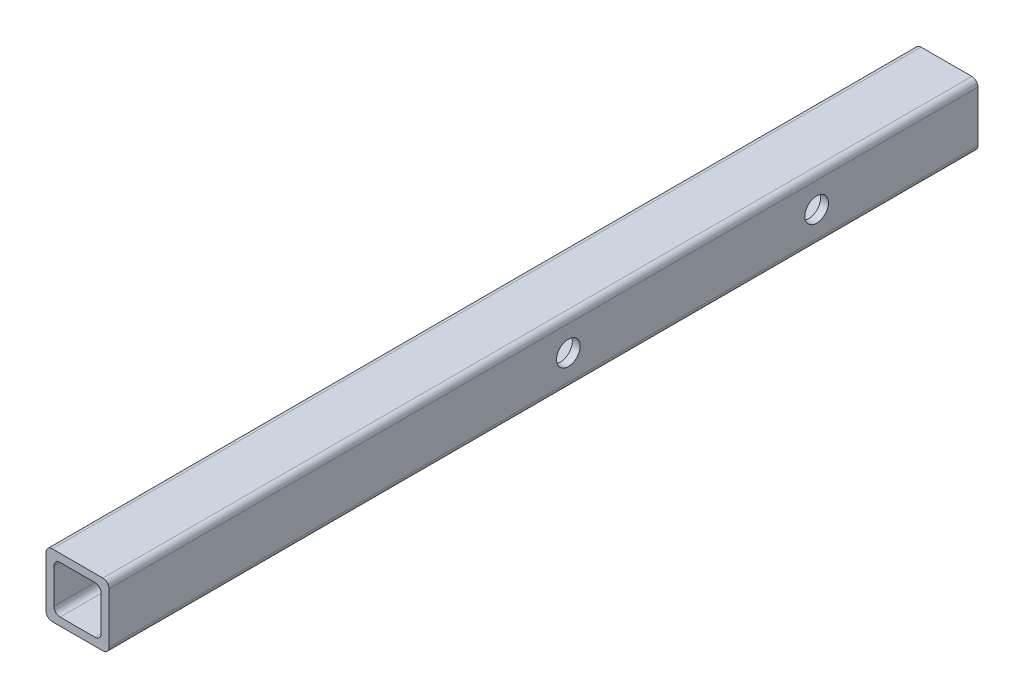
SolidWorks part; units mm, degrees
ref_plane "Alzado" through (0, 0, 0) normal (0, 0, 1) x (1, 0, 0)
ref_plane "Planta" through (0, 0, 0) normal (0, 1, 0) x (1, 0, 0)
ref_plane "Vista lateral" through (0, 0, 0) normal (1, 0, 0) x (0, 0, -1)
sketch "Croquis1" plane through (0, 0, 0) normal (0, 0, 1) x (1, 0, 0)
  line L1 (-7.025, -9.525) -> (7.025, -9.525)
  line L2 (-9.525, -7.025) -> (-9.525, 7.025)
  line L3 (-7.025, 9.525) -> (7.025, 9.525)
  line L4 (9.525, -7.025) -> (9.525, 7.025)
  line L5 (-9.525, -9.525) -> (9.525, 9.525) construction
  line L6 (-9.525, 9.525) -> (9.525, -9.525) construction
  line L7 (-10.2, -12.7) -> (10.2, -12.7)
  line L8 (-12.7, -10.2) -> (-12.7, 10.2)
  line L9 (-10.2, 12.7) -> (10.2, 12.7)
  line L10 (12.7, -10.2) -> (12.7, 10.2)
  line L11 (-12.7, -12.7) -> (12.7, 12.7) construction
  line L12 (-12.7, 12.7) -> (12.7, -12.7) construction
  arc A0 (-7.025, -9.525) -> (-9.525, -7.025) centre (-7.025, -7.025) cw
  arc A1 (7.025, -9.525) -> (9.525, -7.025) centre (7.025, -7.025) ccw
  arc A2 (9.525, 7.025) -> (7.025, 9.525) centre (7.025, 7.025) ccw
  arc A3 (12.7, -10.2) -> (10.2, -12.7) centre (10.2, -10.2) cw
  arc A4 (-10.2, -12.7) -> (-12.7, -10.2) centre (-10.2, -10.2) cw
  arc A5 (12.7, 10.2) -> (10.2, 12.7) centre (10.2, 10.2) ccw
  arc A6 (-9.525, 7.025) -> (-7.025, 9.525) centre (-7.025, 7.025) cw
  arc A7 (-10.2, 12.7) -> (-12.7, 10.2) centre (-10.2, 10.2) ccw
  point P0 (0, 0)
  point P6 (0, 0)
  dimension "D3" = 2.5
  dimension "D1" = 25.4
  dimension "D2" = 3.175
extrude "Saliente-Extruir1" add sketch "Croquis1" along normal blind 350
sketch "Croquis2" plane through (-12.7, 0, 0) normal (-1, 0, 0) x (0, 0, 1)
  circle A0 centre (65, 0) radius 4.7625
  circle A1 centre (165, 0) radius 4.7625
  point P2 (0, 0)
  dimension "D1" = 9.525
  dimension "D2" = 65
  dimension "D3" = 100
extrude "Cortar-Extruir1" cut sketch "Croquis2" against normal through all
